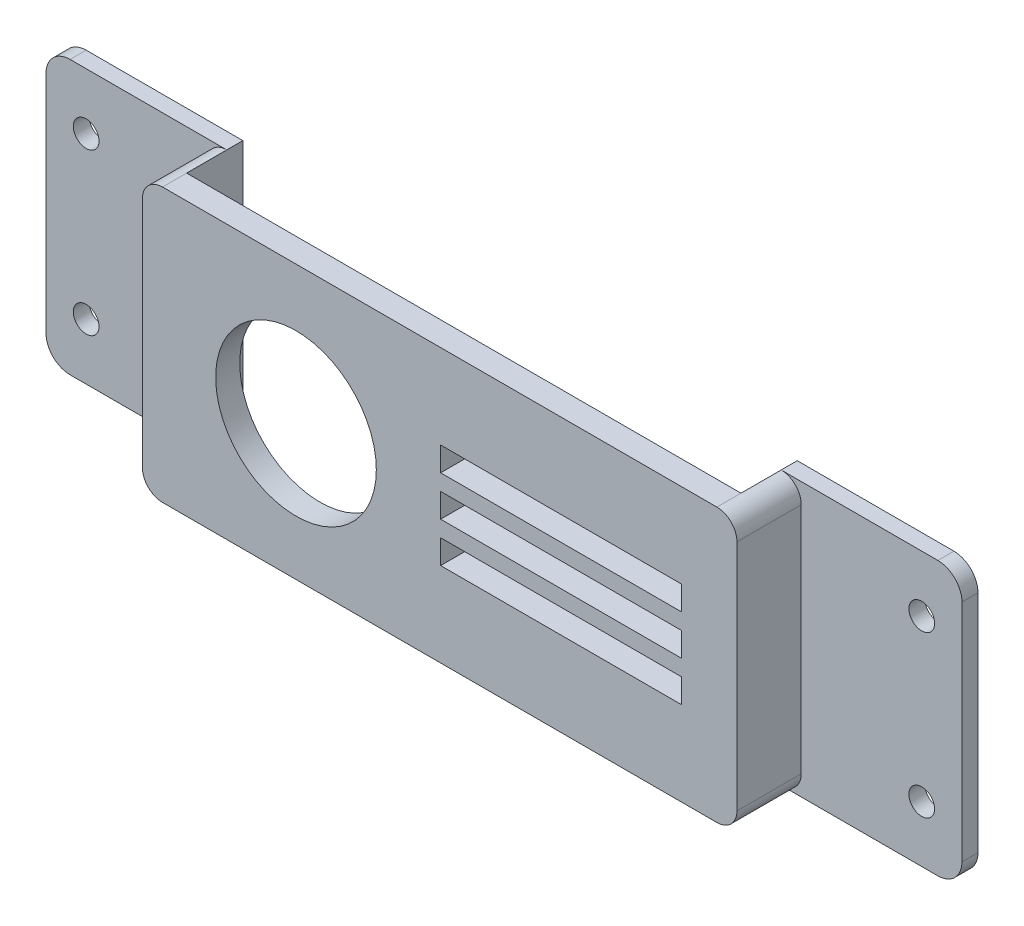
SolidWorks part; units mm, degrees
ref_plane "Front Plane" through (0, 0, 0) normal (0, 0, 1) x (1, 0, 0)
ref_plane "Top Plane" through (0, 0, 0) normal (0, 1, 0) x (1, 0, 0)
ref_plane "Right Plane" through (0, 0, 0) normal (1, 0, 0) x (0, 0, -1)
sketch "Sketch1" plane through (0, 0, 0) normal (0, 0, 1) x (1, 0, 0)
  line L4 (-78.5, 101.2037) -> (-147.5, 101.2037) construction
  line L5 (-75.5, 69.2037) -> (-75.5, 98.2037) construction
  line L6 (-147.5, 66.2037) -> (-78.5, 66.2037) construction
  line L7 (-150.5, 98.2037) -> (-150.5, 69.2037) construction
  line L9 (-150.5, 83.7037) -> (-75.5, 83.7037) construction
  line L10 (-150, 98.2037) -> (-150, 69.2037)
  line L11 (-112.8863, 85.2037) -> (-82.8863, 85.2037)
  line L12 (-112.8863, 85.2037) -> (-112.8863, 82.2037)
  line L13 (-112.8863, 82.2037) -> (-82.8863, 82.2037)
  line L14 (-82.8863, 85.2037) -> (-82.8863, 82.2037)
  line L15 (-112.8863, 87.2037) -> (-82.8863, 87.2037)
  line L16 (-112.8863, 87.2037) -> (-112.8863, 90.2037)
  line L17 (-112.8863, 90.2037) -> (-82.8863, 90.2037)
  line L18 (-82.8863, 87.2037) -> (-82.8863, 90.2037)
  line L19 (-112.8863, 80.2037) -> (-82.8863, 80.2037)
  line L20 (-112.8863, 80.2037) -> (-112.8863, 77.2037)
  line L21 (-112.8863, 77.2037) -> (-82.8863, 77.2037)
  line L22 (-82.8863, 80.2037) -> (-82.8863, 77.2037)
  line L23 (-147.5, 66.7037) -> (-78.5, 66.7037)
  line L24 (-76, 69.2037) -> (-76, 98.2037)
  line L25 (-78.5, 100.7037) -> (-147.5, 100.7037)
  arc A4 (-75.5, 98.2037) -> (-78.5, 101.2037) centre (-78.5, 98.2037) ccw construction
  arc A5 (-78.5, 66.2037) -> (-75.5, 69.2037) centre (-78.5, 69.2037) ccw construction
  arc A6 (-150.5, 69.2037) -> (-147.5, 66.2037) centre (-147.5, 69.2037) ccw construction
  arc A7 (-147.5, 101.2037) -> (-150.5, 98.2037) centre (-147.5, 98.2037) ccw construction
  circle A8 centre (-130.8863, 83.5278) radius 10
  arc A9 (-147.5, 100.7037) -> (-150, 98.2037) centre (-147.5, 98.2037) ccw
  arc A10 (-150, 69.2037) -> (-147.5, 66.7037) centre (-147.5, 69.2037) ccw
  arc A11 (-78.5, 66.7037) -> (-76, 69.2037) centre (-78.5, 69.2037) ccw
  arc A12 (-76, 98.2037) -> (-78.5, 100.7037) centre (-78.5, 98.2037) ccw
  dimension "D1" = 18
  dimension "D2" = 30
  dimension "D3" = 3
  dimension "D4" = 1.5
  dimension "D5" = 3
  dimension "D6" = 3
  dimension "D7" = 2
  dimension "D8" = 2
  dimension "D9" = 0.5
extrude "Boss-Extrude1" add sketch "Sketch1" against normal blind 3
sketch "Sketch3" plane through (0, 0, -3) normal (0, 0, -1) x (-1, 0, 0)
  line L0 (150, 98.2037) -> (150, 69.2037) construction
  line L1 (150, 98.2037) -> (150, 69.2037)
  line L2 (147.5, 100.7037) -> (147.5, 66.7037)
  line L3 (113, 100.7037) -> (113, 66.7037) construction
  line L4 (78.5, 100.7037) -> (147.5, 100.7037) construction
  line L5 (147.5, 66.7037) -> (78.5, 66.7037) construction
  line L6 (78.5, 100.7037) -> (78.5, 66.7037)
  line L7 (76, 98.2037) -> (76, 69.2037)
  arc A0 (147.5, 66.7037) -> (150, 69.2037) centre (147.5, 69.2037) ccw construction
  arc A1 (150, 98.2037) -> (147.5, 100.7037) centre (147.5, 98.2037) ccw construction
  arc A2 (147.5, 66.7037) -> (150, 69.2037) centre (147.5, 69.2037) ccw
  arc A3 (150, 98.2037) -> (147.5, 100.7037) centre (147.5, 98.2037) ccw
  arc A4 (76, 98.2037) -> (78.5, 100.7037) centre (78.5, 98.2037) cw
  arc A5 (78.5, 66.7037) -> (76, 69.2037) centre (78.5, 69.2037) cw
extrude "Boss-Extrude3" add sketch "Sketch3" along normal up to surface (5 mm away)
sketch "Sketch2" plane through (0, 0, -8) normal (0, 0, -1) x (-1, 0, 0)
  line L0 (147.5, 66.7037) -> (78.5, 66.7037) construction
  line L1 (147.5, 100.7037) -> (170, 100.7037)
  line L2 (147.5, 100.7037) -> (147.5, 66.7037)
  line L3 (147.5, 66.7037) -> (170, 66.7037)
  line L4 (170, 100.7037) -> (170, 66.7037)
  line L5 (150, 98.2037) -> (150, 69.2037) construction
  line L6 (113, 100.7037) -> (113, 66.7037) construction
  line L7 (78.5, 100.7037) -> (147.5, 100.7037) construction
  line L8 (56, 100.7037) -> (56, 66.7037)
  line L9 (78.5, 66.7037) -> (56, 66.7037)
  line L10 (78.5, 100.7037) -> (78.5, 66.7037)
  line L11 (78.5, 100.7037) -> (56, 100.7037)
  dimension "D1" = 0
  dimension "D2" = 20
extrude "Boss-Extrude2" add sketch "Sketch2" along normal blind 2
sketch "Sketch4" plane through (0, 0, -10) normal (0, 0, -1) x (-1, 0, 0)
  line L0 (61, 100.6965) -> (61, 66.7134) construction
  line L1 (76, 69.2037) -> (76, 98.2037) construction
  line L2 (78.5, 100.7037) -> (147.5, 100.7037) construction
  line L3 (147.5, 66.7037) -> (78.5, 66.7037) construction
  line L4 (113, 100.7037) -> (113, 66.2037) construction
  line L5 (147.5, 66.2037) -> (78.5, 66.2037) construction
  line L6 (165, 100.6965) -> (165, 66.7134) construction
  circle A0 centre (61, 93.7037) radius 1.6
  circle A1 centre (61, 73.7037) radius 1.6
  circle A2 centre (165, 73.7037) radius 1.6
  circle A3 centre (165, 93.7037) radius 1.6
  dimension "D2" = 3.2
  dimension "D3" = 3.2
  dimension "D4" = 7
  dimension "D1" = 15
  dimension "D5" = 7
extrude "Cut-Extrude1" cut sketch "Sketch4" against normal through all
fillet "Fillet1" radius 3 4 edges at (-170, 66.7037, -9) (-170, 100.7037, -9) (-56, 66.7037, -9) (-56, 100.7037, -9)
